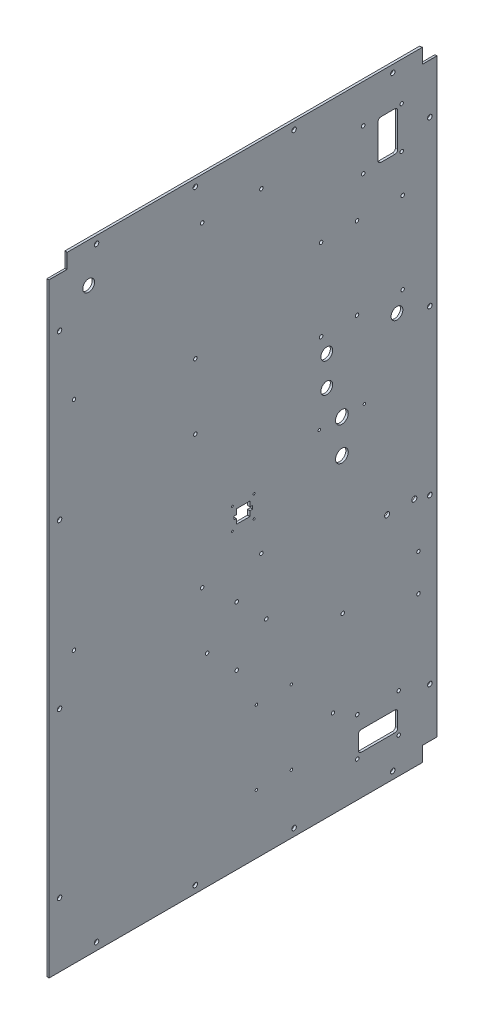
SolidWorks part; units mm, degrees
material "Acrylic (Medium-high impact)"
ref_plane "Front Plane" through (0, 0, 0) normal (0, 0, 1) x (1, 0, 0)
ref_plane "Top Plane" through (0, 0, 0) normal (0, 1, 0) x (1, 0, 0)
ref_plane "Right Plane" through (0, 0, 0) normal (1, 0, 0) x (0, 0, -1)
sketch "Sketch1" plane through (0, 0, 0) normal (1, 0, 0) x (0, 0, -1)
  line L0 (-249.6566, 398.5133) -> (-249.6566, 401.5867) construction
  line L1 (249.6566, -398.5133) -> (-249.6566, -398.5133)
  line L2 (249.6566, -398.5133) -> (249.6566, 398.5133)
  line L3 (249.6566, 398.5133) -> (-249.6566, 398.5133)
  line L4 (-249.6566, -398.5133) -> (-249.6566, 398.5133)
  line L5 (249.6566, -398.5133) -> (-249.6566, 398.5133) construction
  line L6 (249.6566, 398.5133) -> (-249.6566, -398.5133) construction
  line L7 (-249.6566, -398.5133) -> (-249.6566, -411.2133) construction
  line L8 (-249.6566, 398.5133) -> (-252.73, 398.5133) construction
  point P0 (0, 0)
  dimension "D2" = 3.0734
  dimension "D3" = 12.7
  dimension "D4" = 812.8
  dimension "D5" = 3.0734
  dimension "D1" = 502.3866
extrude "SidePanel" add sketch "Sketch1" along normal blind 3.0734
sketch "Sketch2" plane through (3.0734, 0, 0) normal (1, 0, 0) x (0, 0, -1)
  line L0 (192.5066, 398.5133) -> (192.5066, 379.4633) construction
  line L1 (249.6566, 398.5133) -> (-249.6566, 398.5133) construction
  line L2 (249.6566, -398.5133) -> (249.6566, 398.5133) construction
  line L3 (192.5066, -398.5133) -> (192.5066, -379.4633) construction
  line L4 (-249.6566, -398.5133) -> (249.6566, -398.5133) construction
  line L7 (249.6566, 338.1883) -> (230.6066, 338.1883) construction
  circle A0 centre (192.5066, 388.9883) radius 2.8956
  circle A1 centre (192.5066, -388.9883) radius 2.8956
  dimension "D3" = 5.7912
  dimension "D1" = 19.05
  dimension "D4" = 19.05
  dimension "D6" = 19.05
  dimension "D2" = 38.1
extrude "TopBottomHoleMaster" cut sketch "Sketch2" against normal through all
pattern_linear "LPattern1" count 4 spacing 127.0677 along (0, 0, 1) of "TopBottomHoleMaster"
sketch "Sketch3" plane through (3.0734, 0, 0) normal (1, 0, 0) x (0, 0, -1)
  line L1 (249.6566, -398.5133) -> (249.6566, 398.5133) construction
  line L2 (249.6566, 315.8617) -> (230.6066, 315.8617) construction
  line L3 (249.6566, 398.5133) -> (249.6566, 401.5867) construction
  line L4 (249.6566, 398.5133) -> (-249.6566, 398.5133) construction
  line L8 (-245.8466, 315.8617) -> (-226.7966, 315.8617) construction
  line L10 (249.6566, -398.5133) -> (249.6566, 398.5133) construction
  circle A0 centre (-236.3216, 315.8617) radius 2.8956
  circle A1 centre (240.1316, 315.8617) radius 2.8956
  dimension "D5" = 5.7912
  dimension "D2" = 19.05
  dimension "D3" = 3.0734
  dimension "D4" = 85.725
  dimension "D1" = 457.4032
extrude "RearHolesMaster" cut sketch "Sketch3" against normal through all
pattern_linear "LPattern2" count 4 spacing 210.5745 along (0, -1, 0) of "RearHolesMaster"
sketch "Sketch4" plane through (0, 0, 0) normal (-1, 0, 0) x (0, 0, 1)
  line L0 (-249.6566, -398.5133) -> (-249.6566, 398.5133) construction
  line L1 (-249.6566, 398.5133) -> (-230.6066, 398.5133)
  line L2 (-249.6566, 398.5133) -> (-249.6566, 379.4633)
  line L3 (-249.6566, 379.4633) -> (-230.6066, 379.4633)
  line L4 (-230.6066, 398.5133) -> (-230.6066, 379.4633)
  line L5 (249.6566, 398.5133) -> (226.7966, 398.5133)
  line L6 (249.6566, 398.5133) -> (249.6566, 379.4633)
  line L7 (249.6566, 379.4633) -> (226.7966, 379.4633)
  line L8 (226.7966, 398.5133) -> (226.7966, 379.4633)
  line L9 (-249.6566, -398.5133) -> (-230.6066, -398.5133)
  line L10 (-249.6566, -398.5133) -> (-249.6566, -379.4633)
  line L11 (-249.6566, -379.4633) -> (-230.6066, -379.4633)
  line L12 (-230.6066, -398.5133) -> (-230.6066, -379.4633)
  line L13 (249.6566, -398.5133) -> (-249.6566, -398.5133) construction
  line L14 (236.3216, 315.8617) -> (236.3216, 379.4633) construction
  dimension "D1" = 19.05
  dimension "D2" = 9.525
extrude "CornerCuts" cut sketch "Sketch4" against normal through all
hole_wizard "#8 Clearance Hole4 Brain Mount" positions "Sketch13" profile "Sketch14" hole size "#8" standard "ANSI Inch" end condition through all
sketch "Sketch13" plane through (0, 0, 0) normal (-1, 0, 0) x (0, 0, 1)
  line L1 (-23.3934, 344.4367) -> (52.8066, 344.4367) construction
  line L2 (-23.3934, 344.4367) -> (-23.3934, -61.9633) construction
  line L3 (-23.3934, -61.9633) -> (52.8066, -61.9633) construction
  line L4 (52.8066, 344.4367) -> (52.8066, -61.9633) construction
  line L6 (249.6566, 379.4633) -> (249.6566, -398.5133) construction
  line L7 (-230.6066, 398.5133) -> (226.7966, 398.5133) construction
  point P0 (-23.3934, 344.4367)
  point P2 (52.8066, 344.4367)
  point P4 (52.8066, -61.9633)
  point P6 (-23.3934, -61.9633)
  point P78 (-146.4564, 141.8717)
  point P80 (-146.4564, 247.2817)
  point P81 (61.5696, 197.4926)
  point P83 (61.5696, 113.4186)
  dimension "D3" = 196.85
  dimension "D4" = 54.0766
  dimension "D1" = 76.2
  dimension "D2" = 406.4
  dimension "D5" = 123.063
  dimension "D6" = 203.835
  dimension "D7" = 105.41
  dimension "D8" = 84.074
  dimension "D9" = 8.763
  dimension "D10" = 175.3819
sketch "Sketch14" plane through (0, 344.4367, -23.3934) normal (0, 1, 0) x (0, 0, 1)
  line L0 (0, 0) -> (0, 3.0734)
  line L1 (0, 3.0734) -> (2.2479, 3.0734)
  line L2 (2.2479, 3.0734) -> (2.2479, 0)
  line L5 (2.2479, 0) -> (0, 0)
  line L11 (0, -6.35) -> (0, 107.95) construction
  dimension "Thru Hole Dia." = 4.4958
  dimension "Thru Hole Depth" = 3.0734
hole_wizard "#8 Clearance Hole3 Pump Mounts" positions "Sketch15" profile "Sketch16" hole size "#8" standard "ANSI Inch" end condition through all
sketch "Sketch15" plane through (0, 0, 0) normal (-1, 0, 0) x (0, 0, 1)
  line L4 (8.3566, -100.0633) -> (8.3566, -176.2633) construction
  line L5 (8.3566, -100.0633) -> (8.3566, -61.9633) construction
  line L7 (8.3566, -138.1633) -> (46.4566, -138.1633) construction
  line L9 (8.3566, -138.1633) -> (-29.7434, -138.1633) construction
  line L10 (-23.3934, -61.9633) -> (52.8066, -61.9633) construction
  point P0 (46.4566, -138.1633)
  point P2 (8.3566, -100.0633)
  point P4 (8.3566, -176.2633)
  point P6 (-29.7434, -138.1633)
  dimension "D1" = 76.2
  dimension "D2" = 76.2
  dimension "D3" = 38.1
  dimension "D4" = 44.45
sketch "Sketch16" plane through (0, -138.1633, 46.4566) normal (0, 1, 0) x (0, 0, 1)
  line L0 (0, 0) -> (0, 3.0734)
  line L1 (0, 3.0734) -> (2.2479, 3.0734)
  line L2 (2.2479, 3.0734) -> (2.2479, 0)
  line L5 (2.2479, 0) -> (0, 0)
  line L11 (0, -6.35) -> (0, 107.95) construction
  dimension "Thru Hole Dia." = 4.4958
  dimension "Thru Hole Depth" = 3.0734
sketch "Sketch17" plane through (0, 0, 0) normal (-1, 0, 0) x (0, 0, 1)
  line L3 (-230.6066, 379.4633) -> (226.7966, 379.4633) construction
  line L4 (-230.6066, 379.4633) -> (-230.6066, -379.4633) construction
  line L5 (-230.6066, -379.4633) -> (249.6566, -379.4633) construction
  line L6 (-198.8566, 347.7133) -> (-173.4566, 347.7133)
  line L7 (-198.8566, 347.7133) -> (-198.8566, 296.9133)
  line L8 (-198.8566, 296.9133) -> (-173.4566, 296.9133)
  line L9 (-173.4566, 347.7133) -> (-173.4566, 296.9133)
  line L10 (-198.8566, -347.7133) -> (-148.0566, -347.7133)
  line L11 (-198.8566, -347.7133) -> (-198.8566, -322.3133)
  line L12 (-198.8566, -322.3133) -> (-148.0566, -322.3133)
  line L13 (-148.0566, -347.7133) -> (-148.0566, -322.3133)
  line L14 (249.6566, 379.4633) -> (249.6566, -398.5133) construction
  dimension "D1" = 25.4
  dimension "D4" = 50.8
  dimension "D2" = 50.8
  dimension "D3" = 25.4
  dimension "D5" = 31.75
  dimension "D6" = 31.75
  dimension "D7" = 31.75
extrude "Cable Pass Through" cut sketch "Sketch17" against normal through all
hole_wizard "#8 Clearance Hole1 Pass through Mounting holes" positions "Sketch48" profile "Sketch49" hole size "#8" standard "ANSI Inch" end condition through all
sketch "Sketch48" plane through (3.0734, 0, 0) normal (1, 0, 0) x (0, 0, -1)
  line L0 (200.1266, -303.2633) -> (146.7866, -303.2633) construction
  line L3 (146.7866, -352.7933) -> (200.1266, -352.7933) construction
  line L6 (173.4566, -352.7933) -> (173.4566, -303.2633) construction
  line L12 (173.4566, -322.3133) -> (173.4566, -347.7133) construction
  line L13 (148.0566, -322.3133) -> (198.8566, -322.3133) construction
  line L14 (198.8566, -347.7133) -> (148.0566, -347.7133) construction
  line L21 (154.4066, 348.9833) -> (154.4066, 295.6433) construction
  line L24 (203.9366, 348.9833) -> (203.9366, 295.6433) construction
  line L27 (203.9366, 322.3133) -> (154.4066, 322.3133) construction
  line L30 (173.4566, 322.3133) -> (198.8566, 322.3133) construction
  line L31 (173.4566, 296.9133) -> (173.4566, 347.7133) construction
  line L32 (198.8566, 347.7133) -> (198.8566, 296.9133) construction
  line L33 (148.0566, -322.3133) -> (198.8566, -322.3133) construction
  line L34 (173.4566, 296.9133) -> (173.4566, 347.7133) construction
  point P0 (146.7866, -352.7933)
  point P2 (200.1266, -352.7933)
  point P4 (200.1266, -303.2633)
  point P6 (146.7866, -303.2633)
  point P63 (154.4066, 348.9833)
  point P65 (203.9366, 348.9833)
  point P67 (203.9366, 295.6433)
  point P69 (154.4066, 295.6433)
  dimension "D1" = 19.05
  dimension "D2" = 53.34
  dimension "D3" = 5.08
  dimension "D4" = 5.08
  dimension "D5" = 19.05
  dimension "D6" = 53.34
sketch "Sketch49" plane through (3.0734, -352.7933, -146.7866) normal (0, 1, 0) x (0, 0, -1)
  line L0 (0, 0) -> (0, 3.0734)
  line L1 (0, 3.0734) -> (2.2479, 3.0734)
  line L2 (2.2479, 3.0734) -> (2.2479, 0)
  line L5 (2.2479, 0) -> (0, 0)
  line L11 (0, -6.35) -> (0, 107.95) construction
  dimension "Thru Hole Dia." = 4.4958
  dimension "Thru Hole Depth" = 3.0734
hole_wizard "#8 Clearance Hole3 Sensor Mounts" positions "Sketch25" profile "Sketch24" hole size "#8" standard "ANSI Inch"
sketch "Sketch25" plane through (0, 0, 0) normal (-1, 0, 0) x (0, 0, 1)
  line L3 (-21.0566, -36.5633) -> (55.1434, -36.5633) construction
  line L4 (-21.0566, -36.5633) -> (-21.0566, 39.6367) construction
  line L5 (-21.0566, 39.6367) -> (55.1434, 39.6367) construction
  line L6 (55.1434, -36.5633) -> (55.1434, 39.6367) construction
  line L8 (-21.0566, 39.6367) -> (55.1434, 39.6367) construction
  line L9 (-21.0566, 39.6367) -> (-21.0566, 77.7367) construction
  line L10 (-21.0566, 77.7367) -> (55.1434, 77.7367) construction
  line L11 (55.1434, 39.6367) -> (55.1434, 77.7367) construction
  point P38 (55.1434, 39.6367)
  point P135 (-21.0566, 39.6367)
  point P146 (55.1434, 77.7367)
  point P235 (-21.0566, 77.7367)
  dimension "D1" = 76.2
  dimension "D2" = 76.2
  dimension "D3" = 38.1
  dimension "D4" = 76.2
sketch "Sketch24" plane through (0, 39.6367, 55.1434) normal (0, 1, 0) x (0, 0, 1)
  line L0 (0, 0) -> (0, 3.0734)
  line L1 (0, 3.0734) -> (2.2479, 3.0734)
  line L2 (2.2479, 3.0734) -> (2.2479, 0)
  line L5 (2.2479, 0) -> (0, 0)
  line L11 (0, -6.35) -> (0, 107.95) construction
  dimension "Thru Hole Dia." = 4.4958
  dimension "Thru Hole Depth" = 3.0734
sketch "Sketch39" plane through (0, 0, 0) normal (-1, 0, 0) x (0, 0, 1)
  line L0 (-249.6566, 398.5133) -> (-249.6566, 418.9221) construction
  line L1 (-230.2256, 398.5133) -> (-230.6066, 398.5133)
  line L2 (-249.6566, -398.5133) -> (-249.6566, -414.8093) construction
  line L3 (-230.6066, 398.5133) -> (-230.6066, 379.4633)
  line L4 (-230.6066, 379.4633) -> (-249.6566, 379.4633)
  line L5 (-249.6566, 379.0823) -> (-230.2256, 379.0823)
  line L6 (-230.2256, 398.5133) -> (-230.2256, 379.0823)
  line L7 (-249.6566, -398.5133) -> (-270.6931, -398.5133) construction
  line L8 (-249.6566, -379.0823) -> (-249.6566, -379.4633)
  line L9 (-249.6566, -379.4633) -> (-230.6066, -379.4633)
  line L10 (-230.6066, -379.4633) -> (-230.6066, -398.5133)
  line L11 (-249.6566, -379.0823) -> (-230.2256, -379.0823)
  line L12 (-230.2256, -398.5133) -> (-230.2256, -379.0823)
  line L13 (-230.6066, -398.5133) -> (-230.2256, -398.5133)
  line L14 (-249.6566, 379.4633) -> (-249.6566, 379.0823)
  line L15 (226.7966, 398.5133) -> (226.4156, 398.5133)
  line L16 (-230.6066, 398.5133) -> (226.7966, 398.5133) construction
  line L17 (226.4156, 398.5133) -> (226.4156, 379.0823)
  line L18 (249.6566, 379.0823) -> (226.4156, 379.0823)
  line L19 (249.6566, 379.4633) -> (249.6566, -398.5133) construction
  line L20 (226.7966, 398.5133) -> (226.7966, 379.4633)
  line L21 (226.7966, 379.4633) -> (249.6566, 379.4633)
  line L22 (249.6566, 379.4633) -> (249.6566, 379.0823)
  dimension "D1" = 19.431
  dimension "D2" = 19.431
  dimension "D3" = 19.431
  dimension "D4" = 19.431
  dimension "D5" = 0.381
extrude "Cut-Extrude1" cut sketch "Sketch39" against normal blind 2.54
hole_wizard "#8 Clearance Hole -hx mount" positions "Sketch40" profile "Sketch41" hole size "#8" standard "ANSI Inch" end condition through all
sketch "Sketch40" plane through (3.0734, 0, 0) normal (1, 0, 0) x (0, 0, -1)
  line L0 (230.6066, 398.5133) -> (-226.7966, 398.5133) construction
  line L1 (249.6566, -379.4633) -> (249.6566, 379.4633) construction
  point P0 (205.2066, 246.1133)
  point P2 (205.2066, 141.1133)
  point P4 (100.2066, 141.1133)
  point P6 (100.2066, 246.1133)
  dimension "D1" = 152.4
  dimension "D2" = 44.45
  dimension "D3" = 105
  dimension "D4" = 105
sketch "Sketch41" plane through (3.0734, 246.1133, -205.2066) normal (0, 1, 0) x (0, 0, -1)
  line L0 (0, 0) -> (0, 3.0734)
  line L1 (0, 3.0734) -> (2.2479, 3.0734)
  line L2 (2.2479, 3.0734) -> (2.2479, 0)
  line L5 (2.2479, 0) -> (0, 0)
  line L11 (0, -6.35) -> (0, 107.95) construction
  dimension "Thru Hole Dia." = 4.4958
  dimension "Thru Hole Depth" = 3.0734
sketch "Sketch42" plane through (3.0734, 0, 0) normal (1, 0, 0) x (0, 0, -1)
  line L0 (100.2066, 141.1133) -> (205.2066, 141.1133) construction
  line L1 (107.5726, 118.5073) -> (197.8406, 118.5073) construction
  line L2 (152.7066, 141.1133) -> (152.7066, 118.5073) construction
  circle A0 centre (197.8406, 118.5073) radius 7.5787
  circle A1 centre (107.5726, 118.5073) radius 7.5819
  circle A2 centre (197.8406, 118.5073) radius 21.6881 construction
  dimension "D1" = 15.1574
  dimension "D2" = 15.1638
  dimension "D4" = 22.606
  dimension "D3" = 7.366
extrude "Coolant hose pass through" cut sketch "Sketch42" against normal through all
sketch "Sketch43" plane through (3.0734, 0, 0) normal (1, 0, 0) x (0, 0, -1)
  line L0 (-249.6566, 379.4633) -> (-249.6566, -398.5133) construction
  line L1 (230.6066, 398.5133) -> (-226.7966, 398.5133) construction
  line L2 (107.5726, 118.5073) -> (197.8406, 118.5073) construction
  line L3 (107.5726, 118.5073) -> (107.5726, 80.4073) construction
  circle A0 centre (-198.8566, 347.7133) radius 7.5819
  circle A1 centre (107.5726, 80.4073) radius 7.5819
  dimension "D1" = 15.1638
  dimension "D4" = 15.1638
  dimension "D5" = 38.1
  dimension "D2" = 50.8
  dimension "D3" = 50.8
extrude "Air flush in/out" cut sketch "Sketch43" against normal through all
hole_wizard "#8 Clearance Hole2 Air Flush Out mount" positions "Sketch44" profile "Sketch45" hole size "#8" standard "ANSI Inch" end condition through all
sketch "Sketch44" plane through (3.0734, 0, 0) normal (1, 0, 0) x (0, 0, -1)
  line L0 (249.6566, -379.4633) -> (249.6566, 379.4633) construction
  line L1 (-249.6566, -398.5133) -> (230.6066, -398.5133) construction
  point P0 (225.5266, -160.7693)
  point P2 (225.5266, -208.0133)
  point P4 (128.0678, -181.1548)
  dimension "D1" = 47.244
  dimension "D2" = 99.568
  dimension "D3" = 101.092
  dimension "D4" = 24.13
  dimension "D5" = 190.5
sketch "Sketch45" plane through (3.0734, -160.7693, -225.5266) normal (0, 1, 0) x (0, 0, -1)
  line L0 (0, 0) -> (0, 3.0734)
  line L1 (0, 3.0734) -> (2.2479, 3.0734)
  line L2 (2.2479, 3.0734) -> (2.2479, 0)
  line L5 (2.2479, 0) -> (0, 0)
  line L11 (0, -6.35) -> (0, 107.95) construction
  dimension "Thru Hole Dia." = 4.4958
  dimension "Thru Hole Depth" = 3.0734
hole_wizard "#8 Clearance Hole4 Panel Mounts" positions "Sketch46" profile "Sketch47" hole size "#8" standard "ANSI Inch" end condition through all
sketch "Sketch46" plane through (3.0734, 0, 0) normal (1, 0, 0) x (0, 0, -1)
  line L0 (-249.6566, 379.4633) -> (-249.6566, -398.5133) construction
  line L1 (230.6066, 398.5133) -> (-226.7966, 398.5133) construction
  point P0 (-217.7034, 230.1367)
  point P6 (-217.7034, -49.2633)
  dimension "D1" = 31.9532
  dimension "D2" = 168.3766
  dimension "D3" = 279.4
sketch "Sketch47" plane through (3.0734, 230.1367, 217.7034) normal (0, 1, 0) x (0, 0, -1)
  line L0 (0, 0) -> (0, 3.0734)
  line L1 (0, 3.0734) -> (2.2479, 3.0734)
  line L2 (2.2479, 3.0734) -> (2.2479, 0)
  line L5 (2.2479, 0) -> (0, 0)
  line L11 (0, -6.35) -> (0, 107.95) construction
  dimension "Thru Hole Dia." = 4.4958
  dimension "Thru Hole Depth" = 3.0734
fillet "Fillet1" radius 3.81 8 edges at (1.5367, -347.7133, -148.0566) (1.5367, -322.3133, -148.0566) (1.5367, -322.3133, -198.8566) (1.5367, -347.7133, -198.8566) (1.5367, 347.7133, -198.8566) (1.5367, 347.7133, -173.4566) (1.5367, 296.9133, -198.8566) (1.5367, 296.9133, -173.4566)
sketch "Sketch50" plane through (3.0734, 0, 0) normal (1, 0, 0) x (0, 0, -1)
  line L0 (-8.625, 3.8117) -> (8.625, 3.8117)
  line L1 (8.625, 3.8117) -> (8.625, -2.6883)
  line L2 (8.625, -2.6883) -> (12.125, -2.6883)
  line L3 (12.125, -2.6883) -> (12.125, -6.9383)
  line L4 (12.125, -6.9383) -> (8.625, -6.9383)
  line L5 (8.625, -6.9383) -> (8.625, -13.4383)
  line L6 (8.625, -13.4383) -> (-8.625, -13.4383)
  line L7 (-8.625, -13.4383) -> (-8.625, -6.9383)
  line L8 (-8.625, -6.9383) -> (-12.125, -6.9383)
  line L9 (-12.125, -6.9383) -> (-12.125, -2.6883)
  line L10 (-12.125, -2.6883) -> (-8.625, -2.6883)
  line L11 (-8.625, -2.6883) -> (-8.625, 3.8117)
  line L12 (127, -4.8133) -> (127, 38.3667) construction
  line L17 (0, 3.8117) -> (0, -13.4383) construction
  line L18 (-12.125, -4.8133) -> (12.125, -4.8133) construction
  line L19 (-3.4982, 3.8117) -> (-3.4982, -13.4383) construction
  line L20 (127, -4.8133) -> (0, -4.8133) construction
  line L21 (13.97, 9.1567) -> (13.97, -18.7833) construction
  line L22 (-249.6566, -9.525) -> (249.6566, -9.525) construction
  line L23 (98, 38.3667) -> (156, 38.3667) construction
  line L24 (-19.05, 14.2367) -> (19.05, 14.2367) construction
  line L25 (19.05, 14.2367) -> (19.05, -23.8633) construction
  line L26 (-13.97, -18.7833) -> (13.97, -18.7833) construction
  line L27 (-19.05, -23.8633) -> (-19.05, 14.2367) construction
  line L28 (-19.05, -4.8133) -> (19.05, -4.8133) construction
  line L29 (0, 14.2367) -> (0, -23.8633) construction
  line L30 (0, -13.4383) -> (0, -18.7833) construction
  line L31 (-249.6566, -398.5133) -> (230.6066, -398.5133) construction
  line L32 (0, 398.5133) -> (0, -398.5133) construction
  line L41 (230.6066, -379.4633) -> (249.6566, -379.4633)
  line L42 (249.6566, -379.4633) -> (249.6566, 379.4633)
  line L43 (249.6566, 379.4633) -> (230.6066, 379.4633)
  line L44 (230.6066, 379.4633) -> (230.6066, 398.5133)
  line L45 (230.6066, 398.5133) -> (-226.7966, 398.5133)
  line L46 (-226.7966, 398.5133) -> (-226.7966, 379.4633)
  line L47 (-226.7966, 379.4633) -> (-249.6566, 379.4633)
  line L48 (-249.6566, 379.4633) -> (-249.6566, -398.5133)
  line L49 (-249.6566, -398.5133) -> (230.6066, -398.5133)
  line L50 (230.6066, -398.5133) -> (230.6066, -379.4633)
  line L51 (230.6066, -379.4633) -> (249.6566, -379.4633)
  line L52 (249.6566, -379.4633) -> (249.6566, 379.4633)
  line L53 (249.6566, 379.4633) -> (230.6066, 379.4633)
  line L54 (230.6066, 379.4633) -> (230.6066, 398.5133)
  line L55 (230.6066, 398.5133) -> (-226.7966, 398.5133)
  line L56 (-226.7966, 398.5133) -> (-226.7966, 379.4633)
  line L57 (-226.7966, 379.4633) -> (-249.6566, 379.4633)
  line L58 (-249.6566, 379.4633) -> (-249.6566, -398.5133)
  line L59 (-249.6566, -398.5133) -> (230.6066, -398.5133)
  line L60 (230.6066, -398.5133) -> (230.6066, -379.4633)
  circle A0 centre (127, -4.8133) radius 8.1915
  circle A1 centre (127, 38.3667) radius 8.1915
  point P17 (0, 3.8117)
  point P26 (0, -4.8133)
  point P27 (-3.4982, -4.8133)
  point P28 (-13.97, -18.7833)
  point P31 (13.97, -18.7833)
  point P34 (98, 38.3667)
  point P35 (156, 38.3667)
  point P38 (127, 38.3667)
  point P47 (0, -4.8133)
  point P48 (-13.97, 9.1567)
  point P49 (13.97, 9.1567)
  point P52 (13.97, -4.8133)
  point P67 (0, -9.525)
  dimension "D2" = 16.383
  dimension "D19" = 16.383
  dimension "D3" = 17.25
  dimension "D4" = 17.25
  dimension "D7" = 4.25
  dimension "D8" = 24.25
  dimension "D9" = 127
  dimension "D10" = 393.7
  dimension "D12" = 43.18
  dimension "D13" = 58
  dimension "D14" = 38.1
  dimension "D15" = 38.1
  dimension "D16" = 27.94
  dimension "D17" = 27.94
  dimension "D18" = 0
extrude "Sensor Mounting" cut sketch "Sketch50" against normal through all flip side to cut
hole_wizard "#2 Clearance Hole1" positions "Sketch51" profile "Sketch52" hole size "#2" standard "ANSI Inch" end condition through all
sketch "Sketch51" plane through (3.0734, 0, 0) normal (1, 0, 0) x (0, 0, -1)
  point P0 (-13.97, 9.1567)
  point P3 (13.97, 9.1567)
  point P6 (13.97, -18.7833)
  point P9 (-13.97, -18.7833)
sketch "Sketch52" plane through (3.0734, 9.1567, 13.97) normal (0, 1, 0) x (0, 0, -1)
  line L0 (0, 0) -> (0, 3.0734)
  line L1 (0, 3.0734) -> (1.2192, 3.0734)
  line L2 (1.2192, 3.0734) -> (1.2192, 0)
  line L5 (1.2192, 0) -> (0, 0)
  line L11 (0, -6.35) -> (0, 107.95) construction
  dimension "Thru Hole Dia." = 2.4384
  dimension "Thru Hole Depth" = 3.0734
hole_wizard "#4 Clearance Hole2" positions "Sketch53" profile "Sketch54" hole size "#4" standard "ANSI Inch" end condition through all
sketch "Sketch53" plane through (3.0734, 0, 0) normal (1, 0, 0) x (0, 0, -1)
  point P0 (98, 38.3667)
  point P3 (156, 38.3667)
sketch "Sketch54" plane through (3.0734, 38.3667, -98) normal (0, 1, 0) x (0, 0, -1)
  line L0 (0, 0) -> (0, 3.0734)
  line L1 (0, 3.0734) -> (1.6319, 3.0734)
  line L2 (1.6319, 3.0734) -> (1.6319, 0)
  line L5 (1.6319, 0) -> (0, 0)
  line L11 (0, -6.35) -> (0, 107.95) construction
  dimension "Thru Hole Dia." = 3.2639
  dimension "Thru Hole Depth" = 3.0734
fillet "Fillet2" radius 0.127 12 edges at (1.5367, -13.4383, 8.625) (1.5367, -6.9383, -12.125) (1.5367, -13.4383, -8.625) (1.5367, -6.9383, -8.625) (1.5367, -2.6883, -12.125) (1.5367, -2.6883, -8.625) (1.5367, -6.9383, 8.625) (1.5367, -2.6883, 8.625) (1.5367, -2.6883, 12.125) (1.5367, -6.9383, 12.125) (1.5367, 3.8117, -8.625) (1.5367, 3.8117, 8.625)
hole_wizard "#4 Clearance Hole compressor driver" positions "Sketch55" profile "Sketch56" hole size "#4" standard "ANSI Inch" end condition through all
sketch "Sketch55" plane through (0, 0, 0) normal (-1, 0, 0) x (0, 0, 1)
  line L0 (249.6566, -398.5133) -> (-230.2256, -398.5133) construction
  line L2 (249.6566, 379.0823) -> (249.6566, -398.5133) construction
  point P0 (-17.0434, -227.3133)
  point P2 (-62.0434, -227.3133)
  point P4 (-62.0434, -322.3133)
  point P6 (-17.0434, -322.3133)
  dimension "D1" = 45
  dimension "D2" = 95
  dimension "D3" = 76.2
  dimension "D4" = 266.7
sketch "Sketch56" plane through (0, -227.3133, -17.0434) normal (0, 1, 0) x (0, 0, 1)
  line L0 (0, 0) -> (0, 3.0734)
  line L1 (0, 3.0734) -> (1.6319, 3.0734)
  line L2 (1.6319, 3.0734) -> (1.6319, 0)
  line L5 (1.6319, 0) -> (0, 0)
  line L11 (0, -6.35) -> (0, 107.95) construction
  dimension "Thru Hole Dia." = 3.2639
  dimension "Thru Hole Depth" = 3.0734
hole_wizard "1/4 Clearance Hole ball valve u bolt" positions "Sketch57" profile "Sketch58" hole size "1/4" standard "ANSI Inch" end condition through all
sketch "Sketch57" plane through (3.0734, 0, 0) normal (1, 0, 0) x (0, 0, -1)
  line L0 (-249.6566, -398.5133) -> (230.6066, -398.5133) construction
  line L1 (249.6566, -379.4633) -> (249.6566, 379.4633) construction
  point P0 (220.1418, -99.7331)
  point P2 (185.2168, -99.7331)
  dimension "D1" = 298.7802
  dimension "D2" = 29.5148
  dimension "D3" = 34.925
sketch "Sketch58" plane through (3.0734, -99.7331, -220.1418) normal (0, 1, 0) x (0, 0, -1)
  line L0 (0, 0) -> (0, 3.0734)
  line L1 (0, 3.0734) -> (3.2639, 3.0734)
  line L2 (3.2639, 3.0734) -> (3.2639, 0)
  line L5 (3.2639, 0) -> (0, 0)
  line L11 (0, -6.35) -> (0, 107.95) construction
  dimension "Thru Hole Dia." = 6.5278
  dimension "Thru Hole Depth" = 3.0734
hole_wizard "Aeration Pump #8 Clearance Hole1" positions "Sketch59" profile "Sketch60" hole size "#8" standard "ANSI Inch" end condition through all
sketch "Sketch59" plane through (3.0734, 0, 0) normal (1, 0, 0) x (0, 0, -1)
  line L0 (110.7503, -290.9602) -> (141.7066, -290.9602) construction
  line L1 (141.7066, -290.9602) -> (141.7066, -280.6414) construction
  line L2 (141.7066, -280.6414) -> (110.7503, -280.6414) construction
  line L3 (110.7503, -280.6414) -> (110.7503, -290.9602) construction
  line L6 (110.7503, -285.8008) -> (141.7066, -285.8008) construction
  line L9 (115.5129, -280.6414) -> (115.5129, -290.9602) construction
  line L13 (151.8666, -322.3133) -> (195.0466, -322.3133) construction
  line L14 (148.0566, -343.9033) -> (148.0566, -326.1233) construction
  point P0 (115.5128, -285.8008)
  dimension "D1" = 10.3187
  dimension "D2" = 30.9562
  dimension "D3" = 4.7625
  dimension "D4" = 36.5125
  dimension "D5" = 6.35
sketch "Sketch60" plane through (3.0734, -285.8008, -115.5128) normal (0, 1, 0) x (0, 0, -1)
  line L0 (0, 0) -> (0, 3.0734)
  line L1 (0, 3.0734) -> (2.1526, 3.0734)
  line L2 (2.1526, 3.0734) -> (2.1526, 0)
  line L5 (2.1526, 0) -> (0, 0)
  line L11 (0, -6.35) -> (0, 107.95) construction
  dimension "Thru Hole Dia." = 4.3053
  dimension "Thru Hole Depth" = 3.0734
equation "\"Height\"= 32in"
equation "\"Width\"= 23in"
equation "\"Depth\"= 20in"
equation "\"Plexi\"= .121in"
equation "\"Cutwidth\"= .016in"
equation "\"Earsize\"= 1in + \"Cutwidth\" /2"
equation "\"Slotsize\" = 1in - \"CutWidth\" / 2"
equation "\"InnerWidth\" = \"Width\" - 2* \"Plexi\""
equation "\"InnerHeight\" = \"Height\" -2 * \"Plexi\""
equation "\"InnerDepth\" = \"Depth\" - 2*\"Plexi\""
equation "\"RearHoleSpacing\" = (\"Width\" - 2*\"RearHolesBorder\") / (\"RearNumHoles\"-1)"
equation "\"RivetDia\" = .228in"
equation "\"SlotDepth\" = \"Plexi\" + 0.75in + .005in"
equation "\"SideSlotWidth\"   = \"Plexi\"+.005in"
equation "\"SidePanelVertSpacing\" = (\"Height\"-2*(1.75-\"Plexi\")) / 5"
equation "\"BottomPanelSideHoleSpacing\" = (\"InnerDepth\"-2*(1.75-\"Plexi\")) / 4"
equation "\"D1@Sketch1\"=\"TopDepth\""
equation "\"D2@Sketch1\"=\"Plexi\""
equation "\"D1@SidePanel\"=\"Plexi\""
equation "\"MagnetThickness\"= 0.125in"
equation "\"MagnetDiameter\"= 12mm"
equation "\"DoorPlexi\" = \"Plexi\""
equation "\"Boxsize\" = .75in"
equation "\"Boxinner\" = .625in"
equation "\"CornerCube\" = 0.75in"
equation "\"FingerLength\" = 1.125in"
equation "\"RearNumHoles\" = 4"
equation "\"RearHolesBorder\" = 2.25"
equation "\"RearBarLength\" = (\"InnerWidth\"-2*\"CornerCube\")"
equation "\"RearTopNumHoles\" = 4"
equation "\"RearTopHolesBorder\" = 3.1"
equation "\"RearTopHolesSpacing\" = (\"Width\" - 2*\"RearTopHolesBorder\") / (\"RearTopNumHoles\"-1)"
equation "\"SideTopNumHoles\" = 4"
equation "\"SideTopHoleOffset\"=\"CornerCube\"+\"FingerLength\"+\"Plexi\"+.5"
equation "\"SideTopHoleSpacing\" = (\"TopBarDepth\"-2*\"SideTopHoleOffset\") / (\"SideTopNumHoles\"-1)"
equation "\"SideHorizNumHoles\" = 4"
equation "\"SideHorizHoleBorder\" = 1.50"
equation "\"SideHorizHoleSpacing\" = (\"TopBarDepth\"-2*\"SideHorizHoleBorder\") / (\"SideHorizNumHoles\"-1)"
equation "\"SideVertNumHoles\" = 4"
equation "\"SideVertHolesBorder\" = \"CornerCube\"+\"FingerLength\"+1.50"
equation "\"SideVertHoleSpacing\" = (\"SideVertBarLength\" - 2*(\"SideVertHolesBorder\"-\"Plexi\"-\"CornerCube\")) / (\"SideVertNumHoles\"-1)"
equation "\"FrontDoorGap\" = .1in"
equation "\"TopDepth\" = \"Depth\"-\"DoorPlexi\"-\"FrontDoorGap\""
equation "\"TopBarDepth\" = \"Depth\"-\"DoorPlexi\"-\"Plexi\"-2*\"MagnetThickness\"-2*\"CornerCube\""
equation "\"D1@Sketch2\"=\"Boxsize\""
equation "\"D2@Sketch2\"=\"SideHorizHoleBorder\""
equation "\"D3@Sketch2\"=\"RivetDia\""
equation "\"D4@Sketch2\"=\"Boxsize\""
equation "\"D3@LPattern1\"=\"SideHorizHoleSpacing\""
equation "\"D1@LPattern1\"=\"SideHorizNumHoles\""
equation "\"D2@Sketch3\"=\"Boxsize\""
equation "\"D3@Sketch3\"=\"Plexi\""
equation "\"D4@Sketch3\"=\"SideVertHolesBorder\""
equation "\"D5@Sketch3\"=\"RivetDia\""
equation "\"D3@LPattern2\"=\"SideVertHoleSpacing\""
equation "\"D1@LPattern2\"=\"SideVertNumHoles\""
equation "\"BasePlateThickness\" = 0.5in"
equation "\"SideVertBarLength\"=\"Height\"-\"BasePlateThickness\"-2*\"CornerCube\"-\"Plexi\""
equation "\"RearSideVertNumHoles\" = 4"
equation "\"RearSideVertHolesBorder\" = 2.4"
equation "\"RearSideVertHoleSpacing\" = (\"SideVertBarLength\" - 2*(\"RearSideVertHolesBorder\"-\"Plexi\"-\"CornerCube\")) / (\"RearSideVertNumHoles\"-1)"
equation "\"D3@Sketch1\"=\"BasePlateThickness\""
equation "\"D4@Sketch1\"=\"Height\""
equation "\"D6@Sketch2\"=\"CornerCube\""
equation "\"D1@Sketch4\"=\"Boxsize\""
equation "\"D5@Sketch1\"=\"Plexi\""
equation "\"BasePlateWidth\" = \"Width\"+\"EBWidth\"-2*\"Plexi\""
equation "\"BasePlateDepth\" = \"TopBarDepth\"+2*\"CornerCube\""
equation "\"FingerWidth\" = .625in"
equation "\"CoolerDepth\" = 12in"
equation "\"ShelfDepth\" = \"TopBarDepth\"+\"CornerCube\"-\"CoolerDepth\""
equation "\"IntakeWidth\"=4in"
equation "\"IntakeHeight\"=2in"
equation "\"ExhaustWidth\"=4in"
equation "\"ExhaustHeight\"=2in"
equation "\"VentSpacing\"=7in"
equation "\"D1@Sketch3\"=\"TopBarDepth\""
equation "\"BoxsizeHalf\" = \"Boxsize\"/2"
equation "\"D2@Sketch4\"=\"BoxsizeHalf\""
equation "\"EBWidth\" = 9in"
equation "\"ShelfGap\" = 0.5in"
equation "\"ShelfBarDepth\"=\"ShelfDepth\"-2*\"CornerCube\""
equation "\"ShelfWidth\" = \"EBWidth\"-\"ShelfGap\""
equation "\"ShelfBarWidth\" = \"EBWidth\"-\"Boxsize\""
equation "\"ShelfBarWidthShort\" = \"ShelfBarWidth\"-\"Boxsize\"-\"ShelfGap\""
equation "\"VentVertLocation\"=12.75in"
equation "\"AngleBracketLength\"=20mm"
equation "\"AngleBracketWidth\"=.5in"
equation "\"AngleBracketThickness\"=.125in"
equation "\"AngleBracketHolePos\"=15mm"
equation "\"AngleBracketHoleDia\"=\"Rivet3_16Dia\""
equation "\"ShelfBarAngleHole\"=\"ShelfGap\"+\"Boxsize\"+\"AngleBracketHolePosShort\""
equation "\"ComponentMountDia\"=0.1770"
equation "\"ShelfThickness\" = .1250in"
equation "\"Rivet3_16Dia\" = .191in"
equation "\"BinderPostDia\" = .228in"
equation "\"ShelfHeight1\" = 13in"
equation "\"ShelfHeight2\" = 24in"
equation "\"AngleBracketLengthShort\"=.625in"
equation "\"AngleBracketLengthLong\"=1in"
equation "\"AngleBracketHolePosShort\"=.358in"
equation "\"AngleBracketHolePosLong\"=.7in"
equation "\"PSBracketThickness\" = .0641in"
equation "\"EBForwardMountOffset\" = 4.0in"
equation "\"EBForwardMount\" = 2*\"Boxsize\"+\"CoolerDepth\"+\"EBForwardMountOffset\""
equation "\"EBRearwardMountOffset\" = 1.5in"
equation "\"EBRearwardMount\"= \"Boxsize\"+\"EBRearwardMountOffset\""
equation "\"MagSealWidth\" = \"InnerWidth\""
equation "\"MagSealHeight\" = \"Height\"-\"BasePlateThickness\"-\"Plexi\""
equation "\"MagWidth\" = .500in"
equation "\"SiliconeSealOD\" = .3125in"
equation "\"SiliconeSealID\" = .1875in"
equation "\"SiliconeSealWidth\" = \"MagSealWidth\" - 2*\"MagWidth\"-\"SiliconeSealOD\""
equation "\"SiliconeSealHeigth\" = \"MagSealHeight\" - 2*\"MagWidth\"-\"SiliconeSealOD\""
equation "\"HooknLoopThick\" = .085in"
equation "\"HooknLoopWidth\" = 0.75in"
equation "\"HooknLoopHeigth\" = 0.75in"
equation "\"CoolantHosePassThrough\"=0.59675"
equation "\"D1@Sketch42\"=\"CoolantHosePassThrough\""
equation "\"HumiditySensorClearanceHole\"=0.65625"
equation "\"RivNutHeight\" = 0.015in"
